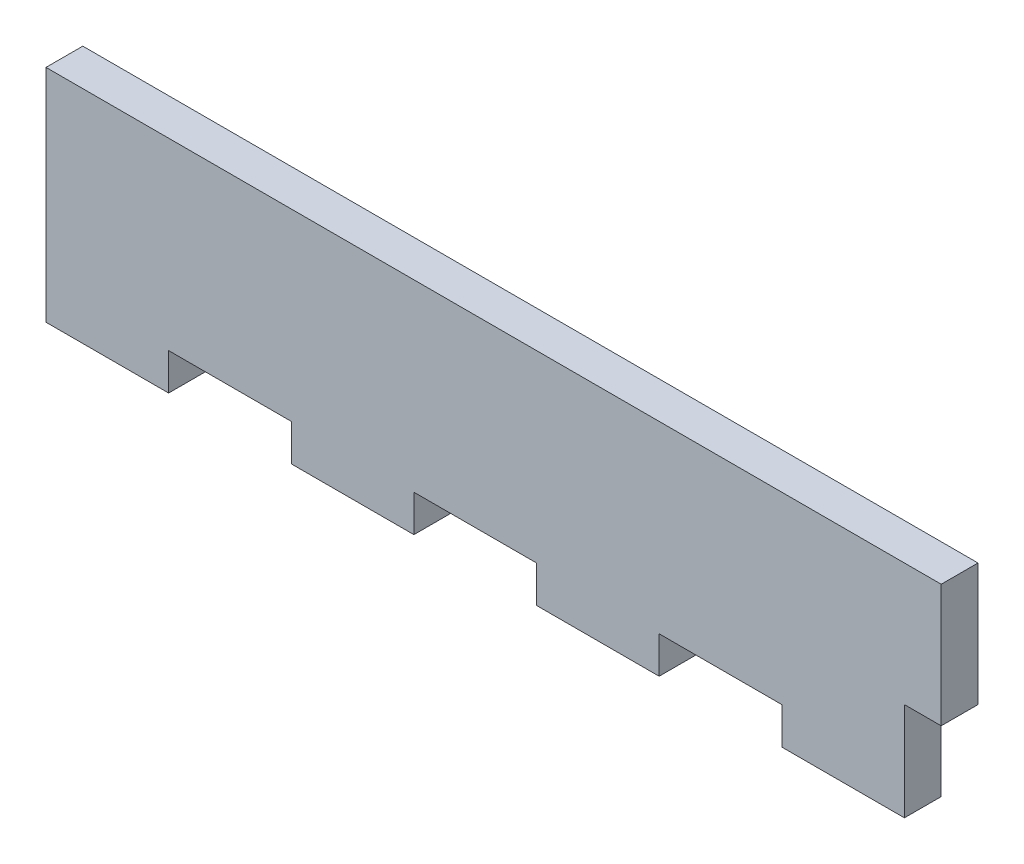
SolidWorks part; units mm, degrees
ref_plane "Plan de face" through (0, 0, 0) normal (0, 0, 1) x (1, 0, 0)
ref_plane "Plan de dessus" through (0, 0, 0) normal (0, 1, 0) x (1, 0, 0)
ref_plane "Plan de droite" through (0, 0, 0) normal (1, 0, 0) x (0, 0, -1)
sketch "Esquisse1" plane through (0, 0, 0) normal (0, 0, 1) x (1, 0, 0)
  line L1 (0, 0) -> (70, 0)
  line L2 (0, 0) -> (0, -18)
  line L3 (0, -18) -> (70, -18)
  line L4 (70, 0) -> (70, -18)
  dimension "D1" = 70
  dimension "D2" = 18
extrude "Boss.-Extru.1" add sketch "Esquisse1" along normal blind 3
sketch "Esquisse2" plane through (0, 0, 3) normal (0, 0, 1) x (1, 0, 0)
  line L0 (0, -18) -> (70, -18) construction
  line L1 (60, -18) -> (50, -18)
  line L2 (60, -18) -> (60, -15)
  line L3 (60, -15) -> (50, -15)
  line L4 (50, -18) -> (50, -15)
  line L5 (70, -18) -> (70, 0) construction
  dimension "D1" = 10
  dimension "D2" = 10
  dimension "D3" = 3
extrude "Enlèv. mat.-Extru.1" cut sketch "Esquisse2" against normal blind 3
pattern_linear "Répétition linéaire1" count 3 spacing 20 along (-1, 0, 0) of "Enlèv. mat.-Extru.1"
sketch "Esquisse3" plane through (70, 0, 0) normal (1, 0, 0) x (0, 0, -1)
  line L0 (0, -18) -> (0, 0) construction
  line L1 (-3, 0) -> (0, 0)
  line L2 (-3, 0) -> (-3, -10)
  line L3 (-3, -10) -> (0, -10)
  line L4 (0, 0) -> (0, -10)
  dimension "D1" = 10
extrude "Boss.-Extru.2" add sketch "Esquisse3" along normal blind 3
